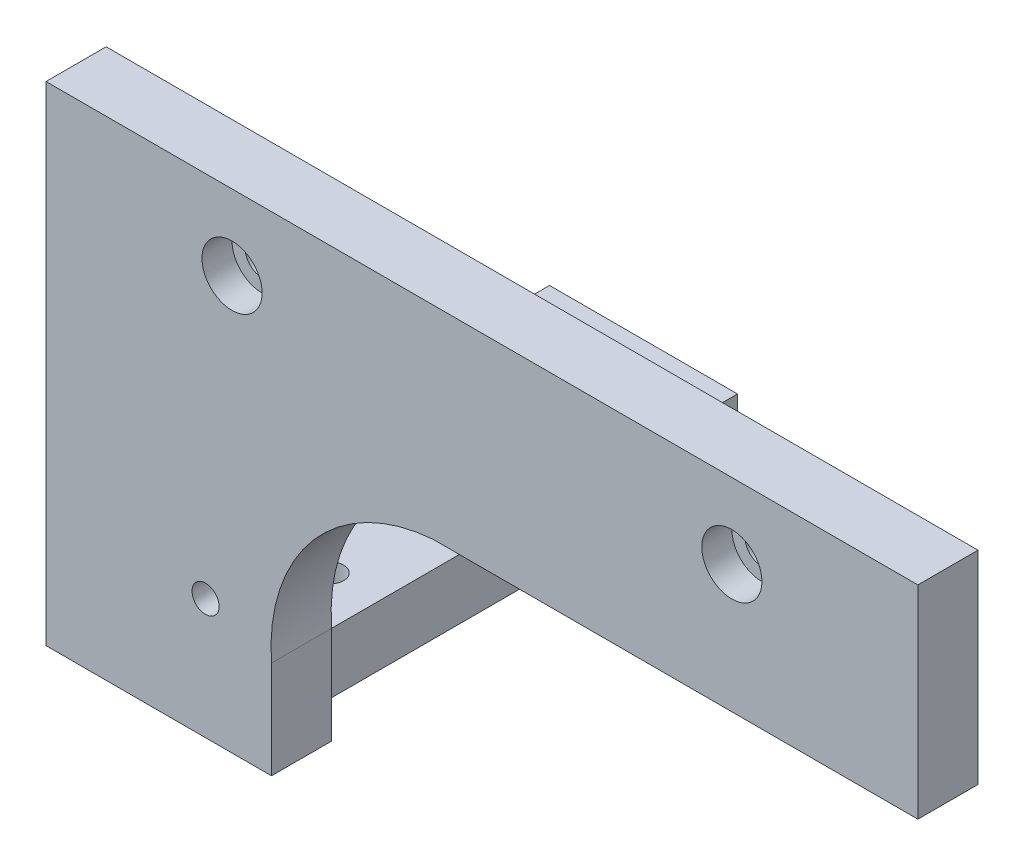
SolidWorks part; units mm, degrees
ref_plane "前视基准面" through (0, 0, 0) normal (0, 0, 1) x (1, 0, 0)
ref_plane "上视基准面" through (0, 0, 0) normal (0, 1, 0) x (1, 0, 0)
ref_plane "右视基准面" through (0, 0, 0) normal (1, 0, 0) x (0, 0, -1)
other "Configuration Table"
sketch "草图1" plane through (0, 0, 0) normal (0, 0, 1) x (1, 0, 0)
  line L4 (58, 13.5) -> (58, -13.5)
  line L7 (-6.5, -13.5) -> (58, -13.5)
  line L11 (-28, -43.5) -> (-28, -38.5)
  line L19 (-58, 13.5) -> (-58, -43.5)
  line L20 (-58, -43.5) -> (-28, -43.5)
  line L21 (-58, 13.5) -> (58, 13.5)
  arc A1 (-6.5, -13.5) -> (-28, -38.5) centre (-4.75, -36.75) ccw
  circle A2 centre (-36.7691, -35.4844) radius 1.8
  point P0 (0, 0)
  point P3 (-36.4628, -38.5)
  point P7 (-36.7691, -35.4844)
extrude "凸台-拉伸1" add sketch "草图1" along normal blind 8
sketch "草图3" plane through (0, 0, 8) normal (0, 0, 1) x (1, 0, 0)
  circle A0 centre (-33.25, 3.5) radius 2.25
  circle A1 centre (33.25, 3.5) radius 2.25
extrude "切除-拉伸1" cut sketch "草图3" against normal through all
sketch "草图5" plane through (0, -43.5, 0) normal (0, -1, 0) x (1, 0, 0)
  line L38 (-33, -59) -> (-58, -59)
  line L39 (-58, 8) -> (-28, 8)
  line L40 (-28, 8) -> (-28, 0)
  line L41 (-58, 8) -> (-58, -59)
  line L42 (-33, -59) -> (-33, -4.5109)
  circle A4 centre (-49.677, -44.8877) radius 1.8
  circle A5 centre (-39.677, -44.8877) radius 1.8
  arc A6 (-28, 0) -> (-33, -4.5109) centre (-28.2446, -4.7554) ccw
extrude "凸台-拉伸3" add sketch "草图5" along normal blind 8
sketch "草图17" plane through (0, -51.5, 0) normal (0, -1, 0) x (1, 0, 0)
  circle A0 centre (-39.4815, -11.2841) radius 1.8
  point P2 (-39.4815, -11.2841)
extrude "切除-拉伸8" cut sketch "草图17" against normal blind 10
sketch "草图18" plane through (0, 0, 8) normal (0, 0, 1) x (1, 0, 0)
  circle A0 centre (-33.25, 3.5) radius 4
  circle A1 centre (33.25, 3.5) radius 4
extrude "切除-拉伸9" cut sketch "草图18" against normal blind 4
